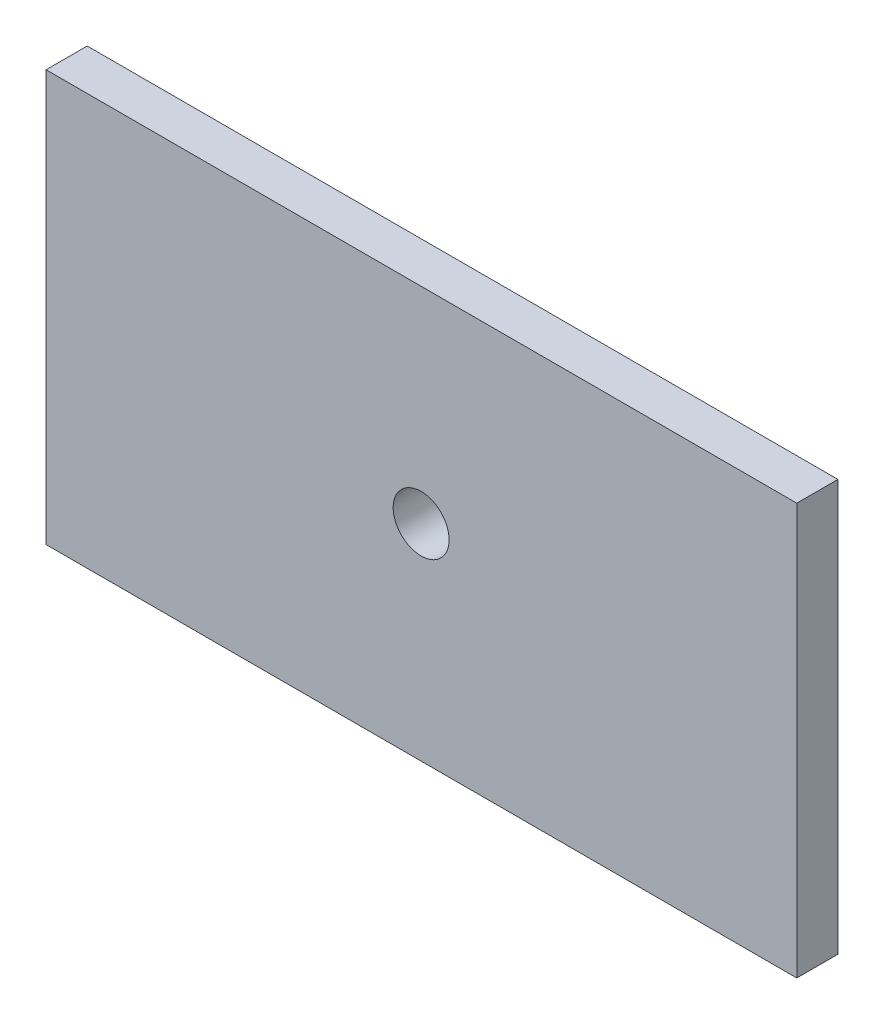
SolidWorks part; units mm, degrees
material "ASTM A36"
ref_plane "Front" through (0, 0, 0) normal (0, 0, 1) x (1, 0, 0)
ref_plane "Top" through (0, 0, 0) normal (0, 1, 0) x (1, 0, 0)
ref_plane "Side" through (0, 0, 0) normal (1, 0, 0) x (0, 0, -1)
sketch "Sketch1" plane through (0, 0, 0) normal (1, 0, 0) x (0, 0, -1)
  line L0 (0, 0) -> (6.35, 0)
  line L1 (6.35, 63.5) -> (0, 63.5)
  line L2 (0, 63.5) -> (0, 0)
  line L3 (6.35, 63.5) -> (6.35, 0)
  dimension "D1" = 6.35
  dimension "D2" = 63.5
extrude "Extrude1" add sketch "Sketch1" along normal blind 115.918
sketch "Sketch2" plane through (0, 0, 0) normal (0, 0, 1) x (1, 0, 0)
  line L0 (115.918, 0) -> (0, 0) construction
  line L2 (0, 63.5) -> (0, 0) construction
  circle A0 centre (57.912, 31.75) radius 4.318
  dimension "D1" = 8.636
  dimension "D2" = 31.75
  dimension "D3" = 57.912
extrude "Cut-Extrude1" cut sketch "Sketch2" against normal blind 12.7
